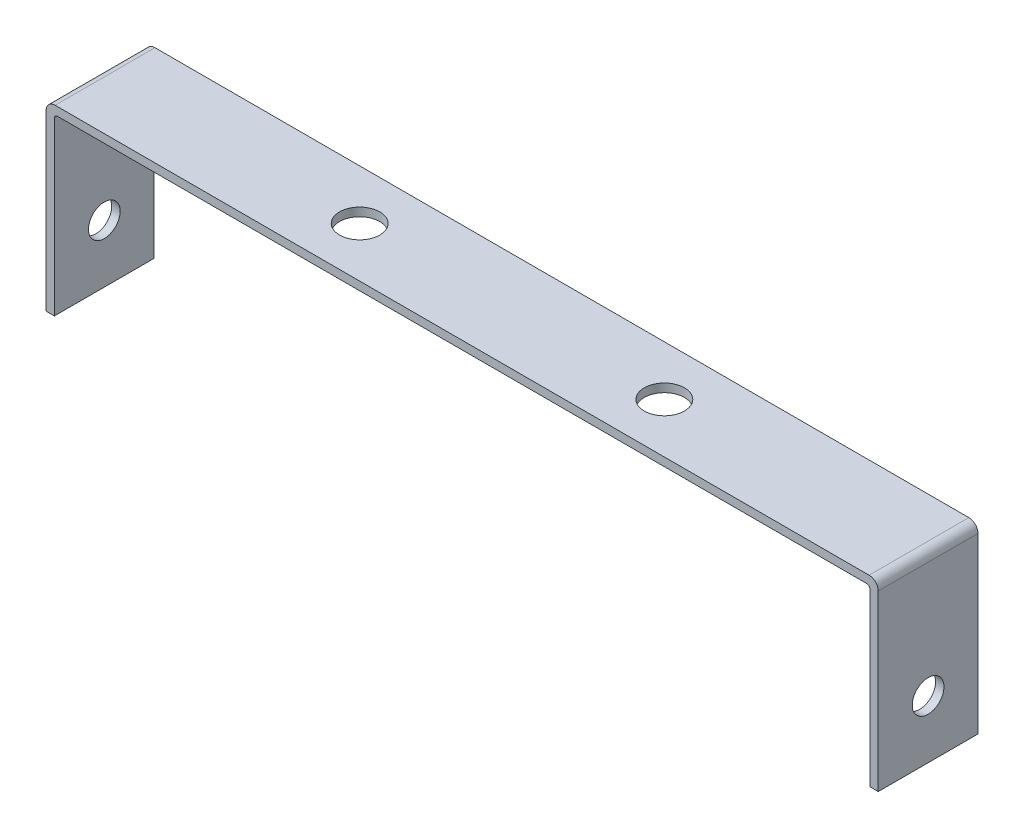
SolidWorks part; units mm, degrees
ref_plane "Front Plane" through (0, 0, 0) normal (0, 0, 1) x (1, 0, 0)
ref_plane "Top Plane" through (0, 0, 0) normal (0, 1, 0) x (1, 0, 0)
ref_plane "Right Plane" through (0, 0, 0) normal (1, 0, 0) x (0, 0, -1)
sketch "Sketch1" plane through (0, 0, 0) normal (0, 1, 0) x (1, 0, 0)
  line L1 (-72.0413, 28.8354) -> (61.7587, 28.8354)
  line L2 (-72.0413, 28.8354) -> (-72.0413, 12.4654)
  line L3 (-72.0413, 12.4654) -> (61.7587, 12.4654)
  line L4 (61.7587, 28.8354) -> (61.7587, 12.4654)
  circle A0 centre (-30.1413, 20.6504) radius 3.3
  circle A1 centre (19.8587, 20.6504) radius 3.3
  dimension "D4" = 6.6
  dimension "D5" = 6.6
  dimension "D1" = 133.8
  dimension "D2" = 16.37
  dimension "D3" = 50
  dimension "D6" = 8.185
  dimension "D7" = 41.9
extrude "Boss-Extrude1" add sketch "Sketch1" along normal blind 1.38
sketch "Sketch2" plane through (0, 1.38, 0) normal (0, 1, 0) x (1, 0, 0)
  line L0 (-72.0413, 12.4654) -> (61.7587, 12.4654) construction
  line L1 (-72.0413, 28.8354) -> (-73.4213, 28.8354)
  line L2 (-72.0413, 28.8354) -> (-72.0413, 12.4654)
  line L3 (-72.0413, 12.4654) -> (-73.4213, 12.4654)
  line L4 (-73.4213, 28.8354) -> (-73.4213, 12.4654)
  line L6 (61.7587, 28.8354) -> (63.1387, 28.8354)
  line L7 (61.7587, 28.8354) -> (61.7587, 12.4654)
  line L8 (61.7587, 12.4654) -> (63.1387, 12.4654)
  line L9 (63.1387, 28.8354) -> (63.1387, 12.4654)
  dimension "D1" = 0
  dimension "D2" = 1.38
  dimension "D3" = 0
  dimension "D4" = 1.38
extrude "Boss-Extrude2" add sketch "Sketch2" against normal blind 30
fillet "Fillet1" radius 1.5 2 edges at (-73.4213, 1.38, -20.6504) (63.1387, 1.38, -20.6504)
fillet "Fillet2" radius 0.5 2 edges
sketch "Sketch3" plane through (-73.4213, 0, 0) normal (-1, 0, 0) x (0, 0, 1)
  line L0 (-28.8354, -28.62) -> (-12.4654, -28.62) construction
  circle A0 centre (-20.6504, -19.12) radius 2.6
  point P2 (-20.6504, -28.62)
  dimension "D1" = 0
  dimension "D2" = 5.2
  dimension "D3" = 9.5
extrude "Cut-Extrude1" cut sketch "Sketch3" against normal through all
